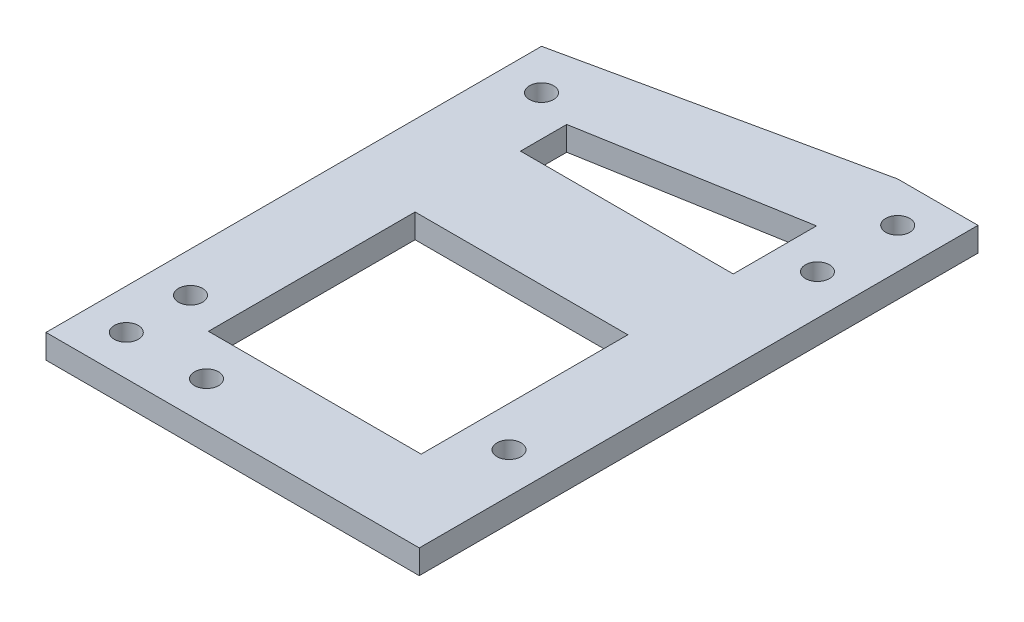
SolidWorks part; units mm, degrees
ref_plane "Front Plane" through (0, 0, 0) normal (0, 0, 1) x (1, 0, 0)
ref_plane "Top Plane" through (0, 0, 0) normal (0, 1, 0) x (1, 0, 0)
ref_plane "Right Plane" through (0, 0, 0) normal (1, 0, 0) x (0, 0, -1)
sketch "Sketch1" plane through (0, 0, 0) normal (0, 1, 0) x (1, 0, 0)
  line L0 (0, 0) -> (0, 10.18) construction
  line L1 (0, 10.18) -> (36.5, 10.18) construction
  line L2 (0, 0) -> (0, 51.73) construction
  line L3 (36.5, 10.18) -> (36.5, 49.6) construction
  line L4 (36.5, 49.6) -> (36.5, 59.6) construction
  line L5 (0, 0) -> (0, -5) construction
  line L6 (5, -5) -> (-5, -5)
  line L7 (0, 51.73) -> (0, 56.73) construction
  line L8 (5, 56.73) -> (-5, 56.73)
  line L9 (-5, 56.73) -> (-5, -5)
  line L10 (5, 56.73) -> (5, -5)
  line L11 (36.5, 59.6) -> (36.5, 64.6) construction
  line L12 (41.5, 64.6) -> (31.5, 64.6)
  line L13 (36.5, 10.18) -> (36.5, -19.82) construction
  line L14 (41.5, -19.82) -> (31.5, -19.82)
  line L15 (31.5, 64.6) -> (31.5, -19.82)
  line L16 (41.5, 64.6) -> (41.5, -19.82)
  line L17 (31.5, 64.6) -> (-5, 56.73)
  line L18 (5, 56.73) -> (31.5, 54.48)
  line L19 (5, -5) -> (31.5, -5)
  line L20 (5, 5.234) -> (31.5, 5.234)
  line L21 (31.5, -5) -> (41.5, -5)
  line L22 (36.5, 10.18) -> (38.7718, 10.18) construction
  line L23 (38.7718, 10.18) -> (38.7718, 11.18) construction
  line L24 (38.7718, 11.18) -> (36.5, 11.18) construction
  circle A0 centre (0, 0) radius 1.5
  circle A2 centre (0, 51.73) radius 1.5
  circle A3 centre (36.5, 49.6) radius 1.5
  circle A4 centre (36.5, 59.6) radius 1.5
  circle A5 centre (36.5, 11.18) radius 1.5
  dimension "D1" = 10.18
  dimension "D2" = 36.5
  dimension "D3" = 51.73
  dimension "D4" = 39.42
  dimension "D5" = 10
  dimension "D6" = 5
  dimension "D7" = 5
  dimension "D8" = 5
  dimension "D9" = 5
  dimension "D10" = 5
  dimension "D11" = 5
  dimension "D12" = 1
extrude "Boss-Extrude1" add sketch "Sketch1" along normal blind 3
sketch "Sketch2" plane through (0, 3, 0) normal (0, 1, 0) x (1, 0, 0)
  line L0 (5, 44.1091) -> (31.5, 44.1091)
  line L1 (5, 56.73) -> (5, 5.234) construction
  line L2 (31.5, 54.48) -> (31.5, 5.234) construction
  line L3 (31.5, 44.1091) -> (31.5, 30.982)
  line L4 (31.5, 30.982) -> (5, 30.982)
  line L5 (5, 30.982) -> (5, 44.1091)
  line L6 (5, 56.73) -> (5, 49.8671)
  line L7 (5, 56.73) -> (5, 5.234) construction
  line L8 (5, 49.8671) -> (31.5, 54.48)
  line L9 (31.5, 54.48) -> (5, 56.73)
extrude "Boss-Extrude2" add sketch "Sketch2" against normal blind 3
sketch "Sketch3" plane through (0, 3, 0) normal (0, 1, 0) x (1, 0, 0)
  line L0 (0, 0) -> (10, 0) construction
  circle A0 centre (10, 0) radius 1.5
  dimension "D1" = 10
extrude "Cut-Extrude1" cut sketch "Sketch3" against normal blind 10
sketch "Sketch4" plane through (0, 3, 0) normal (0, 1, 0) x (1, 0, 0)
  line L0 (0, 0) -> (0, 8) construction
  circle A0 centre (0, 8) radius 1.5
extrude "Cut-Extrude2" cut sketch "Sketch4" against normal blind 10
